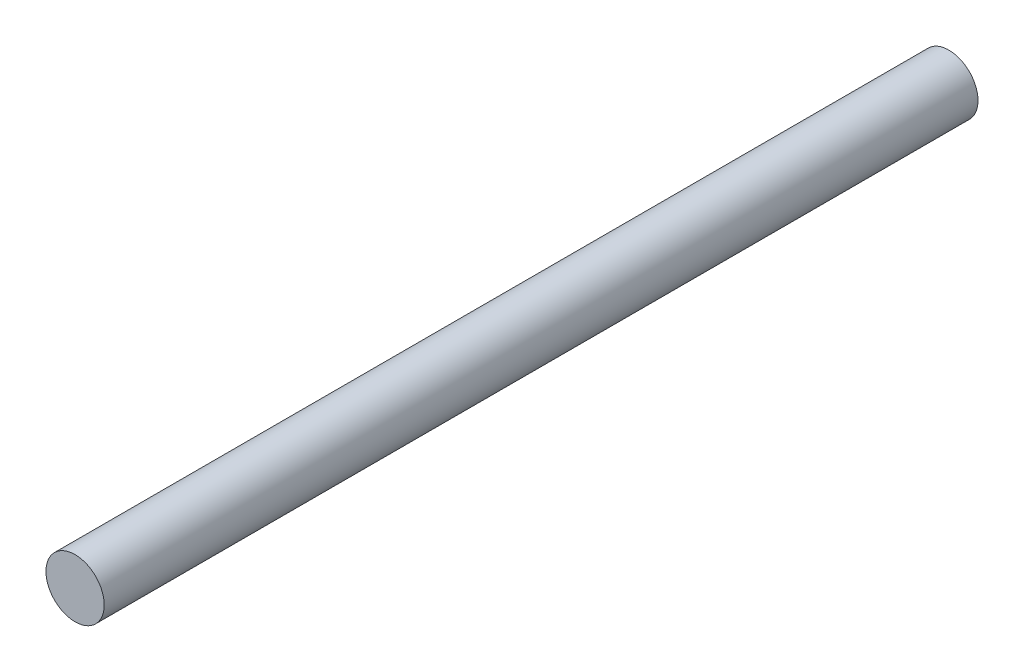
SolidWorks part; units mm, degrees
ref_plane "Plan de face" through (0, 0, 0) normal (0, 0, 1) x (1, 0, 0)
ref_plane "Plan de dessus" through (0, 0, 0) normal (0, 1, 0) x (1, 0, 0)
ref_plane "Plan de droite" through (0, 0, 0) normal (1, 0, 0) x (0, 0, -1)
sketch "Esquisse1" plane through (0, 0, 0) normal (0, 1, 0) x (1, 0, 0)
  line L0 (4, 0) -> (0, 0)
  line L1 (0, 0) -> (0, -120)
  line L2 (0, -120) -> (4, -120)
  line L3 (4, -120) -> (4, 0)
  line L4 (0, 0) -> (0, -120) construction
  dimension "D1" = 120
  dimension "D2" = 4
revolve "Révolution1" add sketch "Esquisse1" angle 360 about L4
